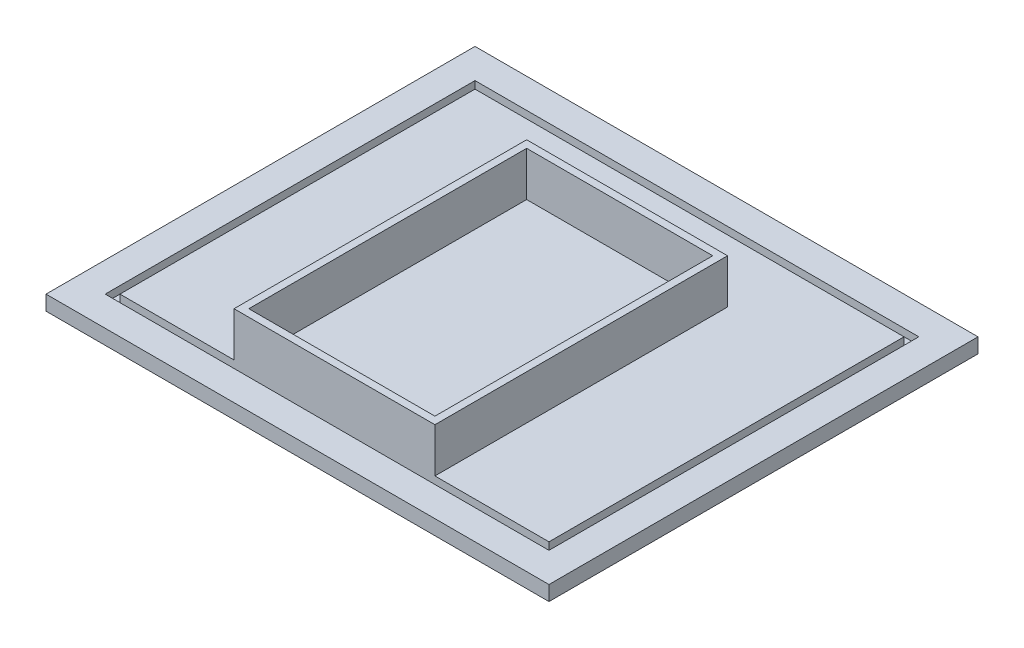
SolidWorks part; units mm, degrees
ref_plane "Front Plane" through (0, 0, 0) normal (0, 0, 1) x (1, 0, 0)
ref_plane "Top Plane" through (0, 0, 0) normal (0, 1, 0) x (1, 0, 0)
ref_plane "Right Plane" through (0, 0, 0) normal (1, 0, 0) x (0, 0, -1)
sketch "Sketch1" plane through (0, 0, 0) normal (0, 1, 0) x (1, 0, 0)
  line L0 (-85, -72.5) -> (-85, 72.5)
  line L1 (0, 0) -> (85, 0) construction
  line L2 (0, 0) -> (0, 72.5) construction
  line L3 (-85, 72.5) -> (85, 72.5)
  line L4 (85, -72.5) -> (85, 72.5)
  line L5 (-85, -72.5) -> (85, -72.5)
  point P9 (-85, 0)
  dimension "D1" = 170
  dimension "D2" = 145
extrude "Boss-Extrude1" add sketch "Sketch1" along normal blind 5
sketch "Sketch2" plane through (0, 5, 0) normal (0, 1, 0) x (1, 0, 0)
  line L0 (85, 72.5) -> (-85, 72.5) construction
  line L1 (0, 0) -> (75, 0) construction
  line L2 (0, 0) -> (0, 62.5) construction
  line L3 (-75, 62.5) -> (75, 62.5)
  line L4 (75, -62.5) -> (75, 62.5)
  line L5 (85, -72.5) -> (85, 72.5) construction
  line L6 (-75, -62.5) -> (-75, 62.5)
  line L7 (-75, -62.5) -> (75, -62.5)
  line L8 (-72.5, 60) -> (72.5, 60)
  line L9 (72.5, 60) -> (72.5, -60)
  line L10 (-72.5, 60) -> (-72.5, -60)
  line L11 (-72.5, -60) -> (72.5, -60)
  point P12 (-75, 0)
  point P17 (72.5, 0)
  point P18 (0, 60)
  point P20 (-72.5, 0)
  dimension "D1" = 10
  dimension "D2" = 10
  dimension "D3" = 2.5
  dimension "D4" = 2.5
extrude "Cut-Extrude1" cut sketch "Sketch2" against normal blind 2.5
sketch "Sketch4" plane through (0, 5, 0) normal (0, 1, 0) x (1, 0, 0)
  line L0 (31.45, -57.5) -> (31.45, 36.4)
  line L1 (31.45, -57.5) -> (-31.45, -57.5)
  line L2 (0, -57.5) -> (0, 36.4) construction
  line L3 (31.45, 36.4) -> (-31.45, 36.4)
  line L4 (-31.45, -57.5) -> (-31.45, 36.4)
  line L5 (33.95, -60) -> (33.95, 38.9)
  line L6 (33.95, -60) -> (-33.95, -60)
  line L7 (0, -60) -> (0, 38.9) construction
  line L8 (33.95, 38.9) -> (-33.95, 38.9)
  line L9 (-33.95, -60) -> (-33.95, 38.9)
  line L10 (-72.5, -60) -> (72.5, -60) construction
  dimension "D1" = 93.9
  dimension "D2" = 62.9
  dimension "D3" = 2.5
  dimension "D4" = 2.5
  dimension "D5" = 2.5
extrude "Boss-Extrude2" add sketch "Sketch4" along normal blind 15
